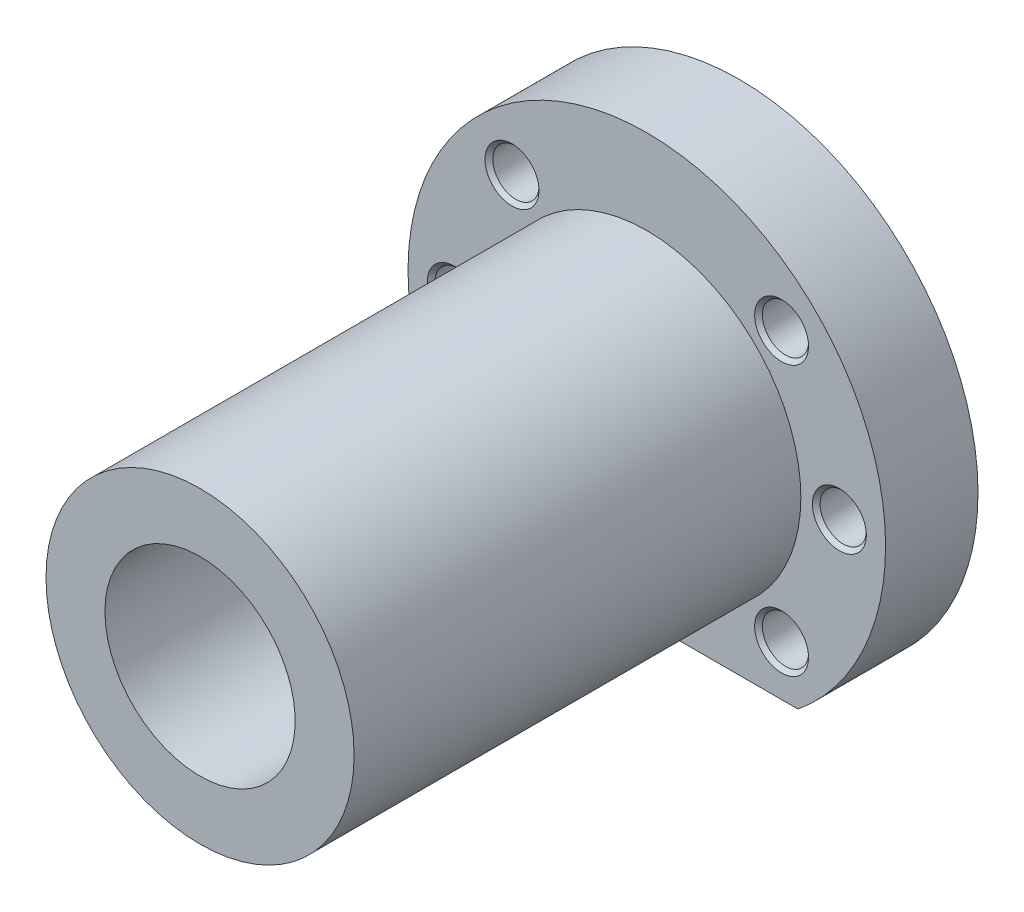
SolidWorks part; units mm, degrees
ref_plane "Płaszczyzna przednia" through (0, 0, 0) normal (0, 0, 1) x (1, 0, 0)
ref_plane "Płaszczyzna górna" through (0, 0, 0) normal (0, 1, 0) x (1, 0, 0)
ref_plane "Płaszczyzna prawa" through (0, 0, 0) normal (1, 0, 0) x (0, 0, -1)
sketch "Szkic1" plane through (0, 0, 0) normal (0, 0, 1) x (1, 0, 0)
  circle A0 centre (0, 0) radius 20
  dimension "D1" = 40
extrude "Dodanie-wyciągnięcie1" add sketch "Szkic1" along normal blind 58
sketch "Szkic3" plane through (0, 0, 0) normal (0, 0, -1) x (-1, 0, 0)
  circle A0 centre (0, 0) radius 31
  dimension "D1" = 62
extrude "Dodanie-wyciągnięcie2" add sketch "Szkic3" along normal blind 12
sketch "Szkic4" plane through (0, 0, -12) normal (0, 0, -1) x (-1, 0, 0)
  line L1 (-19.6214, -24) -> (19.6214, -24)
  line L2 (-19.6214, -24) -> (-19.6214, -31)
  line L3 (-19.6214, -31) -> (19.6214, -31)
  line L4 (19.6214, -24) -> (19.6214, -31)
  circle A0 centre (0, 0) radius 31 construction
  point P6 (0, 0)
  point P7 (0, 0)
  dimension "D1" = 7
extrude "Wytnij-wyciągnięcie1" cut sketch "Szkic4" against normal blind 12
sketch "Szkic5" plane through (0, 0, -12) normal (0, 0, -1) x (-1, 0, 0)
  circle A0 centre (0, 0) radius 12.35
  dimension "D1" = 24.7
extrude "Wytnij-wyciągnięcie2" cut sketch "Szkic5" against normal blind 70
sketch "Szkic6" plane through (0, 0, -12) normal (0, 0, -1) x (-1, 0, 0)
  circle A0 centre (-17.5, 17.5) radius 3
  circle A1 centre (-25, 0) radius 3
  circle A2 centre (-17.5, -17.5) radius 3
  circle A3 centre (17.5, -17.5) radius 3
  circle A4 centre (25, 0) radius 3
  circle A5 centre (17.5, 17.5) radius 3
  dimension "D1" = 17.5
  dimension "D7" = 6
  dimension "D8" = 6
  dimension "D9" = 6
  dimension "D10" = 6
  dimension "D11" = 6
  dimension "D12" = 6
  dimension "D2" = 17.5
  dimension "D3" = 35
  dimension "D4" = 50
  dimension "D5" = 17.5
  dimension "D6" = 25
extrude "Wytnij-wyciągnięcie3" cut sketch "Szkic6" against normal blind 12
chamfer "Sfazowanie1" distance 0.5 angle 45 12 edges at (-28, 0, 0) (-20.5, -17.5, 0) (14.5, -17.5, 0) (22, 0, 0) (14.5, 17.5, 0) (-20.5, 17.5, 0) (14.5, 17.5, -12) (22, 0, -12) (14.5, -17.5, -12) (-20.5, -17.5, -12) (-28, 0, -12) (-20.5, 17.5, -12)
